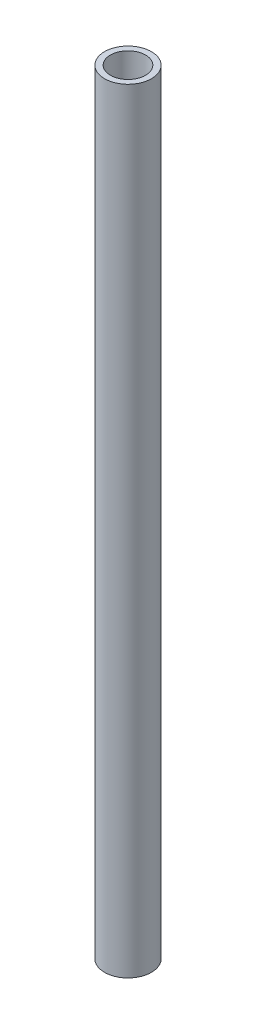
SolidWorks part; units mm, degrees
ref_plane "Front Plane" through (0, 0, 0) normal (0, 0, 1) x (1, 0, 0)
ref_plane "Top Plane" through (0, 0, 0) normal (0, 1, 0) x (1, 0, 0)
ref_plane "Right Plane" through (0, 0, 0) normal (1, 0, 0) x (0, 0, -1)
sketch "Sketch1" plane through (0, 0, 0) normal (0, 1, 0) x (1, 0, 0)
  circle A0 centre (-391.1817, 212.7433) radius 12.7
  circle A1 centre (-391.1817, 212.7433) radius 9.525
  dimension "D1" = 19.05
  dimension "D2" = 25.4
extrude "Boss-Extrude2" add sketch "Sketch1" along normal blind 419.1
